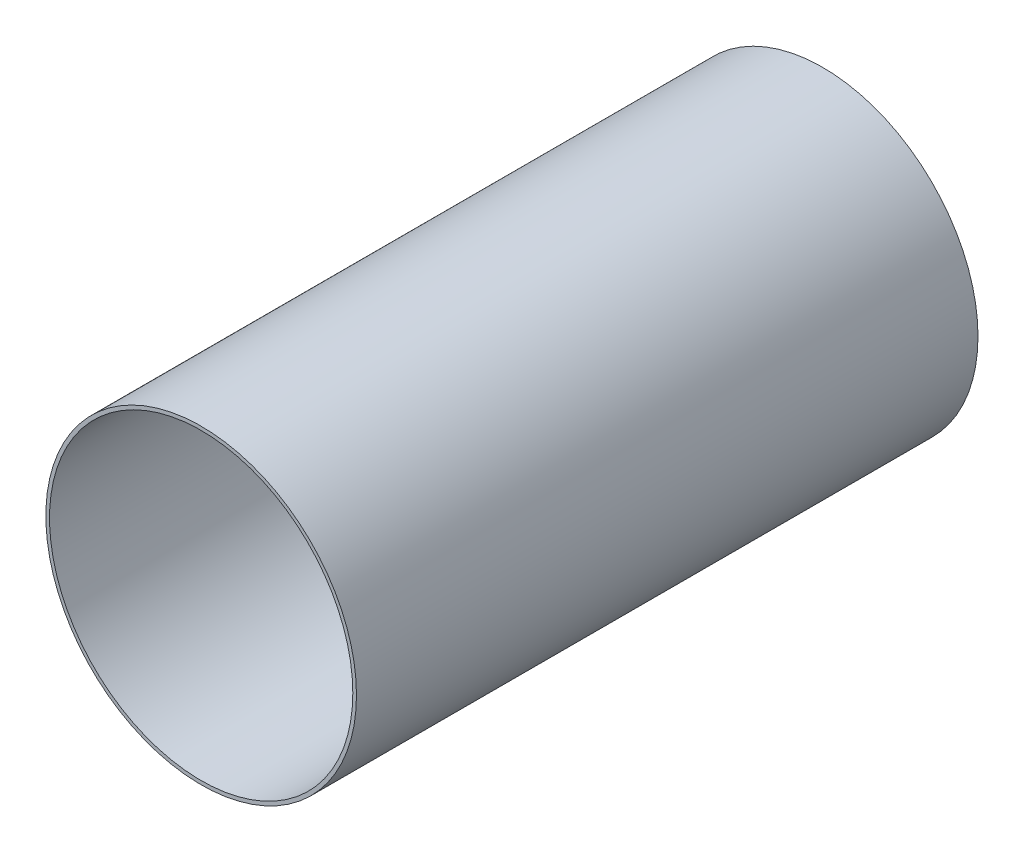
SolidWorks part; units mm, degrees
ref_plane "Front Plane" through (0, 0, 0) normal (0, 0, 1) x (1, 0, 0)
ref_plane "Top Plane" through (0, 0, 0) normal (0, 1, 0) x (1, 0, 0)
ref_plane "Right Plane" through (0, 0, 0) normal (1, 0, 0) x (0, 0, -1)
sketch "Sketch1" plane through (0, 0, 0) normal (0, 0, 1) x (1, 0, 0)
  circle A0 centre (0, 0) radius 63.4746
  circle A1 centre (0, 0) radius 61.976
  dimension "D1" = 123.952
  dimension "D2" = 126.9492
extrude "Boss-Extrude1" add sketch "Sketch1" along normal mid plane 254
equation "\"AIRFRAME_OD\"= 5.15in"
equation "\"AIRFRAME_ID\"= 5.00in"
equation "\"FLAT_T\"= 0.125in"
equation "\"NOSE_EXP_L\"= 27in"
equation "\"NOSE_SHOULDER_L\"= 5in"
equation "\"MAIN_L\"= 30in"
equation "\"RECO_COUP_L\"= 10in"
equation "\"RECO_SWITCH_L\"= 2in"
equation "\"DROGUE_L\"= 20in"
equation "\"ATS_FORE_COUP_L\"= 5.5in"
equation "\"ATS_AFT_COUP_L\"= 4.5in"
equation "\"LOWER_L\"= 30in"
equation "\"FIN_N\"= 4"
equation "\"CR_AFT_X\"= 0.5in"
equation "\"CR_FORE_X\"= 9.25in"
equation "\"D1@Sketch1\"=\"COUPLER_ID\""
equation "\"D2@Sketch1\"=\"COUPLER_OD\""
equation "\"D1@Boss-Extrude1\"=\"RECO_COUP_L\""
equation "\"FIN_ROOT\"= 8in"
equation "\"FIN_X\"= 0.75in"
equation "\"MOTOR_OD\"= 3.091in"
equation "\"MOTOR_ID\"= 3.00in"
equation "\"COUPLER_OD\"= 4.998in"
equation "\"COUPLER_ID\"= 4.88in"
equation "\"RECO_ROD_X\"= 3.5in"
equation "\"ATS_ROD_X\"= 3.75in"
equation "\"MOTOR_L\"= 14in"
equation "\"MOTOR_LOWER_X\"= 2in"
